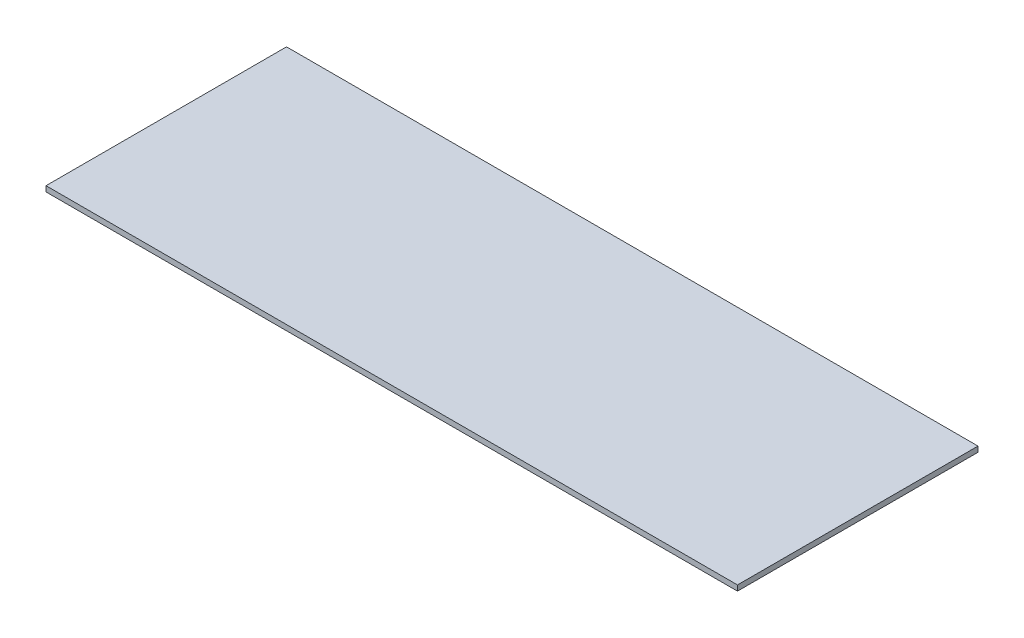
SolidWorks part; units mm, degrees
material "ABS"
ref_plane "Front Plane" through (0, 0, 0) normal (0, 0, 1) x (1, 0, 0)
ref_plane "Top Plane" through (0, 0, 0) normal (0, 1, 0) x (1, 0, 0)
ref_plane "Right Plane" through (0, 0, 0) normal (1, 0, 0) x (0, 0, -1)
sketch "Sketch1" plane through (0, 0, 0) normal (0, 1, 0) x (1, 0, 0)
  line L1 (0, 0) -> (2300, 0)
  line L2 (0, 0) -> (0, 800)
  line L3 (0, 800) -> (2300, 800)
  line L4 (2300, 0) -> (2300, 800)
  dimension "D1" = 800
  dimension "D2" = 2300
extrude "Boss-Extrude1" add sketch "Sketch1" along normal blind 18
